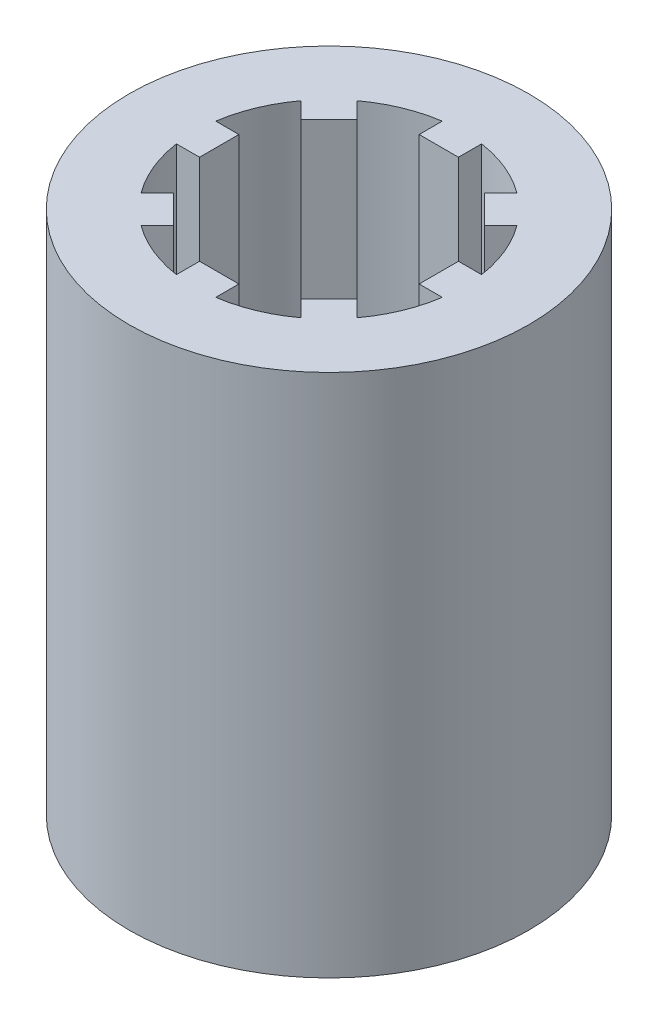
SolidWorks part; units mm, degrees
ref_plane "Front Plane" through (0, 0, 0) normal (0, 0, 1) x (1, 0, 0)
ref_plane "Top Plane" through (0, 0, 0) normal (0, 1, 0) x (1, 0, 0)
ref_plane "Right Plane" through (0, 0, 0) normal (1, 0, 0) x (0, 0, -1)
sketch "Sketch3" plane through (0, 0, 0) normal (0, 1, 0) x (1, 0, 0)
  line L2 (1.905, 12.8774) -> (1.905, 10.6362)
  line L3 (1.905, 10.6362) -> (-1.905, 10.6362)
  line L4 (-1.905, 12.8774) -> (-1.905, 10.6362)
  line L5 (1.905, 15.3987) -> (-1.905, 10.6362) construction
  line L6 (1.905, 10.6362) -> (-1.905, 15.3987) construction
  line L7 (10.4527, 7.7586) -> (8.868, 6.1739)
  line L8 (8.868, 6.1739) -> (6.1739, 8.868)
  line L9 (7.7586, 10.4527) -> (6.1739, 8.868)
  line L11 (12.8774, -1.905) -> (10.6362, -1.905)
  line L12 (10.6362, -1.905) -> (10.6362, 1.905)
  line L13 (12.8774, 1.905) -> (10.6362, 1.905)
  line L15 (7.7586, -10.4527) -> (6.1739, -8.868)
  line L16 (6.1739, -8.868) -> (8.868, -6.1739)
  line L17 (10.4527, -7.7586) -> (8.868, -6.1739)
  line L19 (-1.905, -12.8774) -> (-1.905, -10.6362)
  line L20 (-1.905, -10.6362) -> (1.905, -10.6362)
  line L21 (1.905, -12.8774) -> (1.905, -10.6362)
  line L23 (-10.4527, -7.7586) -> (-8.868, -6.1739)
  line L24 (-8.868, -6.1739) -> (-6.1739, -8.868)
  line L25 (-7.7586, -10.4527) -> (-6.1739, -8.868)
  line L27 (-12.8774, 1.905) -> (-10.6363, 1.905)
  line L28 (-10.6363, 1.905) -> (-10.6362, -1.905)
  line L29 (-12.8774, -1.905) -> (-10.6362, -1.905)
  line L31 (-7.7586, 10.4527) -> (-6.1739, 8.868)
  line L32 (-6.1739, 8.868) -> (-8.868, 6.1739)
  line L33 (-10.4527, 7.7586) -> (-8.868, 6.1739)
  line L41 (0, 0) -> (0, 20.8399) construction
  line L42 (-1.905, 15.3987) -> (-1.905, 12.8774) construction
  line L43 (-1.905, 15.3987) -> (1.905, 15.3987) construction
  line L44 (1.905, 15.3987) -> (1.905, 12.8774) construction
  line L45 (0, 0) -> (25.1483, 0) construction
  line L46 (0, 0) -> (0, -21.283) construction
  circle A0 centre (0, 0) radius 19.3675
  arc A1 (-12.8774, -1.905) -> (-10.4527, -7.7586) centre (0, 0) ccw
  arc A2 (-10.4527, 7.7586) -> (-12.8774, 1.905) centre (0, 0) ccw
  arc A3 (-1.905, 12.8774) -> (-7.7586, 10.4527) centre (0, 0) ccw
  arc A4 (7.7586, 10.4527) -> (1.905, 12.8774) centre (0, 0) ccw
  arc A5 (12.8774, 1.905) -> (10.4527, 7.7586) centre (0, 0) ccw
  arc A6 (10.4527, -7.7586) -> (12.8774, -1.905) centre (0, 0) ccw
  arc A7 (1.905, -12.8774) -> (7.7586, -10.4527) centre (0, 0) ccw
  arc A8 (-7.7586, -10.4527) -> (-1.905, -12.8774) centre (0, 0) ccw
  point P4 (0, 13.0175)
  point P16 (10.6362, 0)
  point P22 (0, -10.6362)
  point P39 (0, 0)
  dimension "D1" = 26.035
  dimension "D2" = 6.35
  dimension "D3" = 3.81
  dimension "D5" = 4.7625
  dimension "D4" = 8
extrude "Boss-Extrude2" add sketch "Sketch3" along normal blind 50.8
